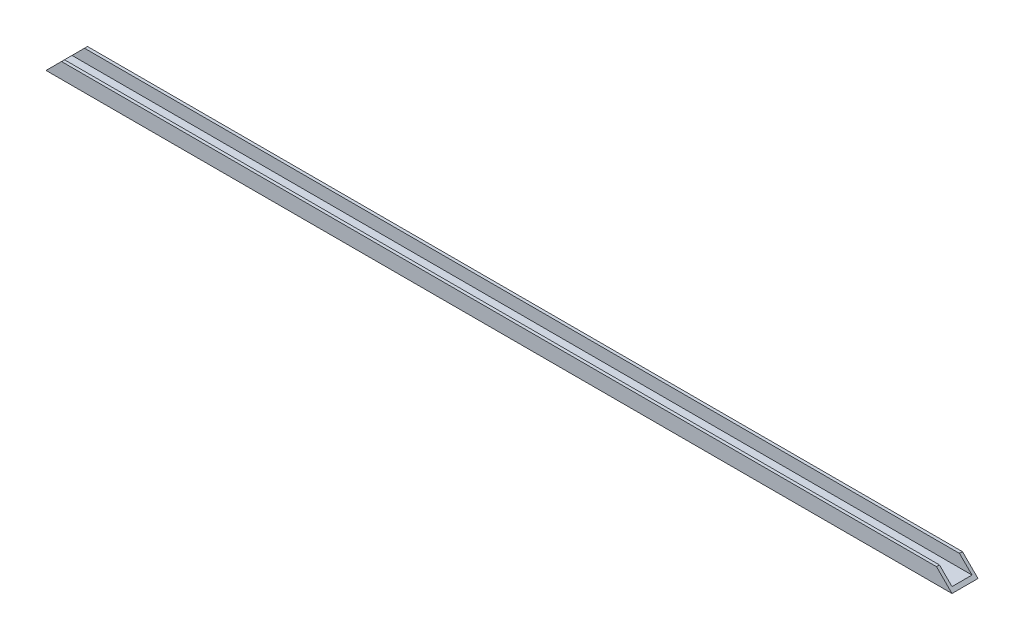
SolidWorks part; units mm, degrees
ref_plane "Front Plane" through (0, 0, 0) normal (0, 0, 1) x (1, 0, 0)
ref_plane "Top Plane" through (0, 0, 0) normal (0, 1, 0) x (1, 0, 0)
ref_plane "Right Plane" through (0, 0, 0) normal (1, 0, 0) x (0, 0, -1)
sketch "Sketch1" plane through (0, 0, 0) normal (1, 0, 0) x (0, 0, -1)
  line L0 (-4, 5) -> (-4, 0)
  line L1 (-4, 0) -> (4, 0)
  line L2 (4, 0) -> (4, 5)
  line L3 (-5.2, 5) -> (-5.2, -1.2)
  line L4 (-5.2, -1.2) -> (5.2, -1.2)
  line L5 (5.2, -1.2) -> (5.2, 5)
  line L6 (-5.2, 5) -> (-4, 5)
  line L7 (4, 5) -> (5.2, 5)
  point P2 (0, 0)
  dimension "D1" = 5
  dimension "D2" = 5
  dimension "D3" = 8
  dimension "D4" = 1.2
  dimension "D5" = 1.2
  dimension "D6" = 1.2
extrude "Boss-Extrude1" add sketch "Sketch1" along normal mid plane 362.4
sketch "Sketch3" plane through (0, 0, 5.2) normal (0, 0, 1) x (1, 0, 0)
  line L0 (-181.2, 5) -> (-181.2, -1.2)
  line L1 (-181.2, -1.2) -> (-175, 5)
  line L2 (181.2, 5) -> (-181.2, 5) construction
  line L3 (-175, 5) -> (-181.2, 5)
  line L4 (0, 32.8147) -> (0, -57.253) construction
  line L5 (181.2, 5) -> (181.2, -1.2)
  line L6 (175, 5) -> (181.2, 5)
  line L7 (181.2, -1.2) -> (175, 5)
  dimension "D1" = 45
extrude "Cut-Extrude1" cut sketch "Sketch3" against normal through all
